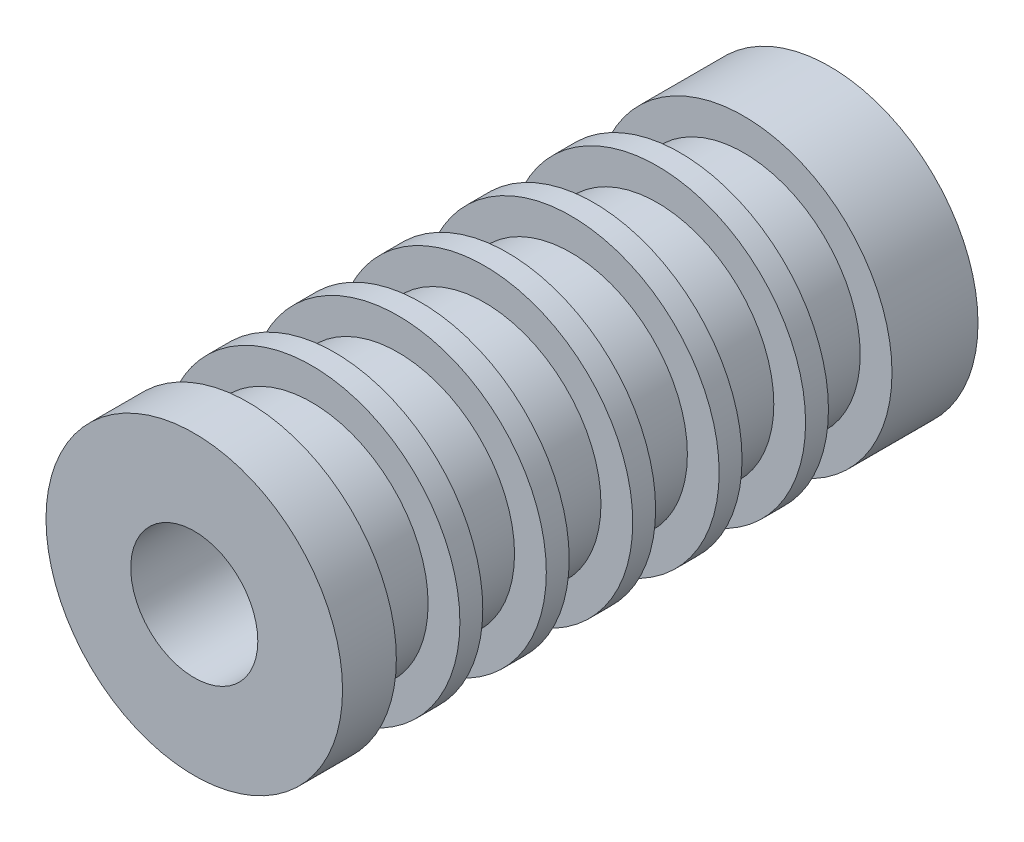
SolidWorks part; units mm, degrees
material "AISI 304"
ref_plane "Front Plane" through (0, 0, 0) normal (0, 0, 1) x (1, 0, 0)
ref_plane "Top Plane" through (0, 0, 0) normal (0, 1, 0) x (1, 0, 0)
ref_plane "Right Plane" through (0, 0, 0) normal (1, 0, 0) x (0, 0, -1)
sketch "Sketch1" plane through (0, 0, 0) normal (0, 0, 1) x (1, 0, 0)
  circle A0 centre (0, 0) radius 11.1125
  circle A1 centre (0, 0) radius 3.2004
  dimension "OD" = 22.225
  dimension "ID" = 6.4008
extrude "Extrude1" add sketch "Sketch1" along normal mid plane 50.8
sketch "Sketch2" plane through (0, 0, 0) normal (1, 0, 0) x (0, 0, -1)
  line L0 (-25.4, -3.2004) -> (25.4, -3.2004) construction
  line L3 (25.4, 3.2004) -> (-25.4, 3.2004) construction
  line L5 (-25.4, -3.2004) -> (25.4, -3.2004)
  line L6 (25.4, 3.2004) -> (-25.4, 3.2004)
sketch "Sketch4" plane through (0, 0, 25.4) normal (0, 0, 1) x (1, 0, 0)
  line L0 (0, 0) -> (-2.263, 2.263)
  line L1 (0, -8.7312) -> (0, 8.7312) construction
  circle A0 centre (0, 0) radius 3.2004 construction
  dimension "D1" = 45
sketch "Sketch5" plane through (0, 0, 25.4) normal (0, 0, 1) x (1, 0, 0)
  circle A0 centre (0, 0) radius 3.2004 construction
  circle A1 centre (0, 0) radius 11.1125
  circle A2 centre (0, 0) radius 11.1125
  circle A3 centre (0, 0) radius 3.2004
  dimension "D1" = 0
extrude "Cut-Extrude1" cut sketch "Sketch5" against normal blind 3.175
sketch "Sketch6" plane through (0, 0, 22.225) normal (0, 0, 1) x (1, 0, 0)
  circle A0 centre (0, 0) radius 4.7625
  dimension "D1" = 9.525
extrude "Cut-Extrude2" cut sketch "Sketch6" against normal through all
sketch "Sketch7" plane through (0, 0, -25.4) normal (0, 0, -1) x (-1, 0, 0)
  circle A0 centre (0, 0) radius 8.7312
  circle A1 centre (0, 0) radius 11.1125 construction
  circle A2 centre (0, 0) radius 11.1125
  dimension "D1" = 17.4625
extrude "Cut-Extrude3" cut sketch "Sketch7" against normal blind 4.7625 from offset 6.4452 offset against normal yes
pattern_linear "LPattern1" count 6 spacing 6.477 along (0, 0, 1) of "Cut-Extrude3"
